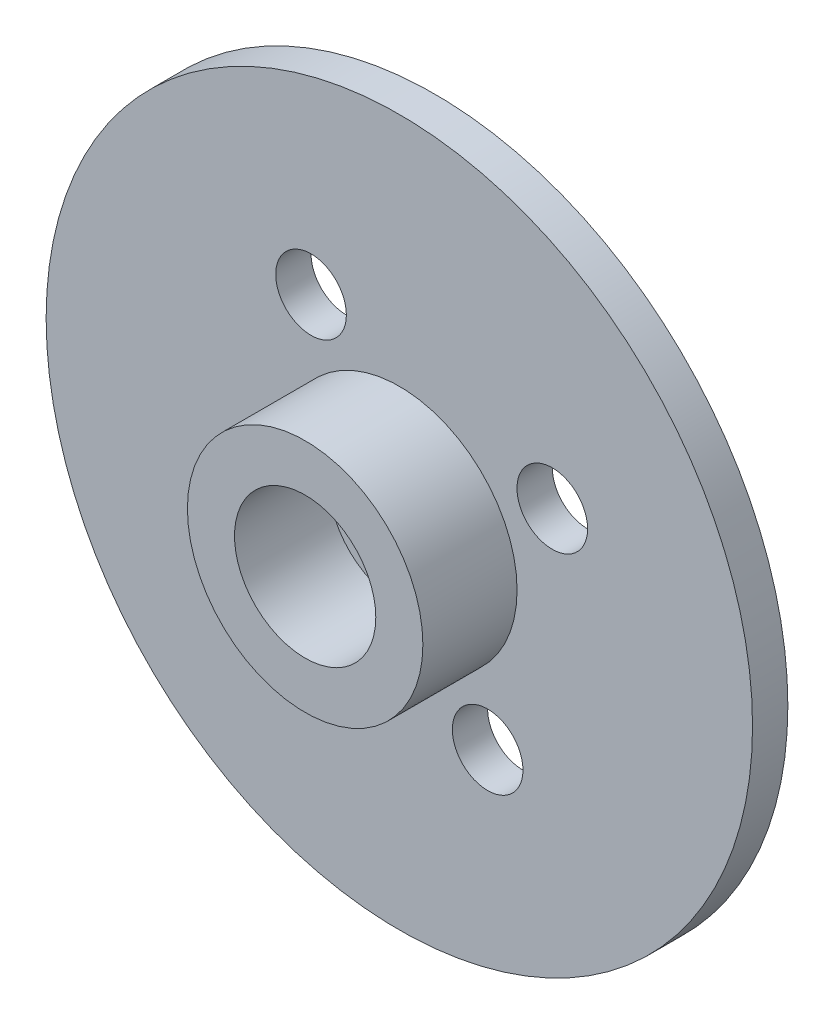
SolidWorks part; units mm, degrees
ref_plane "Front Plane" through (0, 0, 0) normal (0, 0, 1) x (1, 0, 0)
ref_plane "Top Plane" through (0, 0, 0) normal (0, 1, 0) x (1, 0, 0)
ref_plane "Right Plane" through (0, 0, 0) normal (1, 0, 0) x (0, 0, -1)
sketch "Sketch1" plane through (0, 0, 0) normal (0, 0, 1) x (1, 0, 0)
  line L0 (-32.9497, 71.5444) -> (-39.4449, 67.7944) construction
  line L1 (-39.4449, 67.7944) -> (-45.9401, 64.0444) construction
  line L2 (-39.4449, 67.7944) -> (-35.6949, 61.2992) construction
  line L3 (-39.4449, 67.7944) -> (-43.1949, 74.2896) construction
  circle A0 centre (-39.4449, 67.7944) radius 15
  circle A3 centre (-32.9497, 71.5444) radius 1.5
  circle A6 centre (-45.9401, 64.0444) radius 1.5
  circle A7 centre (-39.4449, 67.7944) radius 1
  circle A8 centre (-35.6949, 61.2992) radius 1.5
  circle A9 centre (-43.1949, 74.2896) radius 1.5
  dimension "D1" = 3
extrude "Boss-Extrude1" add sketch "Sketch1" along normal blind 1.5
sketch "Sketch2" plane through (0, 0, 1.5) normal (0, 0, 1) x (1, 0, 0)
  circle A0 centre (-39.4449, 67.7944) radius 3
  circle A1 centre (-39.4449, 67.7944) radius 5
  dimension "D1" = 10
extrude "Boss-Extrude2" add sketch "Sketch2" along normal blind 4
